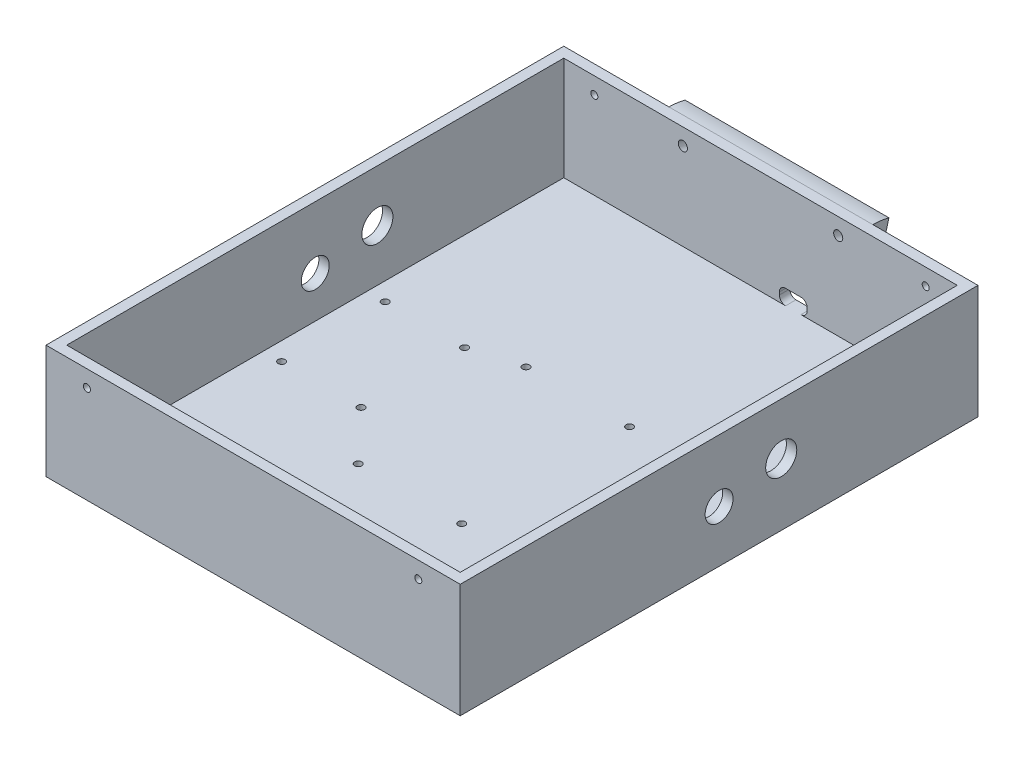
SolidWorks part; units mm, degrees
material "PLA 20%"
ref_plane "Front Plane" through (0, 0, 0) normal (0, 0, 1) x (1, 0, 0)
ref_plane "Top Plane" through (0, 0, 0) normal (0, 1, 0) x (1, 0, 0)
ref_plane "Right Plane" through (0, 0, 0) normal (1, 0, 0) x (0, 0, -1)
sketch "Sketch1" plane through (0, 0, 0) normal (0, 0, 1) x (1, 0, 0)
  line L0 (0, 50) -> (0, 0) construction
  line L1 (-95, 0) -> (95, 0)
  line L2 (-95, 0) -> (-95, 50)
  line L3 (-95, 50) -> (95, 50)
  line L4 (95, 0) -> (95, 50)
  dimension "D1" = 190
  dimension "D2" = 50
extrude "Boss-Extrude1" add sketch "Sketch1" along normal mid plane 240
shell "Shell1" thickness 5
sketch "Sketch3" plane through (100, 0, 0) normal (1, 0, 0) x (0, 0, -1)
  line L0 (-125, -5) -> (125, -5) construction
  line L1 (-15, -5) -> (15, -5)
  line L2 (-15, -5) -> (-15, 30)
  line L3 (-15, 30) -> (15, 30) construction
  line L4 (15, -5) -> (15, 30)
  line L5 (0, 30) -> (0, 20) construction
  line L6 (9.0631, 24.2262) -> (-0.618, 44.9873)
  line L7 (-15, 28.5056) -> (-9.0631, 15.7738)
  circle A0 centre (0, 20) radius 6.75
  arc A1 (-15, 30) -> (15, 30) centre (0, 30) cw
  circle A2 centre (0, 20) radius 10
  dimension "D2" = 13.5
  dimension "D5" = 20
  dimension "D1" = 25
  dimension "D3" = 30
  dimension "D4" = 10
  dimension "D6" = 25
extrude "Cut-Extrude2" cut sketch "Sketch3" against normal through all both and the other way through all contours A0
hole_wizard "M3 Clearance Hole1" positions "Sketch4" profile "Sketch5" hole size "M3" standard "ANSI Metric" end condition through all
sketch "Sketch4" plane through (0, 0, 125) normal (0, 0, 1) x (1, 0, 0)
  point P0 (-80.25, 42)
  point P1 (79.75, 42)
sketch "Sketch5" plane through (-80.25, 42, 125) normal (1, 0, 0) x (0, -1, 0)
  line L0 (0, 0) -> (0, 250)
  line L1 (0, 250) -> (1.7, 250)
  line L2 (1.7, 250) -> (1.7, 0)
  line L3 (1.7, 0) -> (0, 0)
  line L4 (0, -6.35) -> (0, 107.95) construction
  dimension "Thru Hole Dia." = 3.4
  dimension "Thru Hole Depth" = 250
sketch "Sketch8" plane through (0, 0, 0) normal (1, 0, 0) x (0, 0, -1)
  circle A0 centre (30, 25) radius 7.5
  dimension "D1" = 15
  dimension "D2" = 25
  dimension "D3" = 30
extrude "Cut-Extrude4" cut sketch "Sketch8" against normal through all both and the other way through all
sketch "Sketch10" plane through (0, 0, -125) normal (0, 0, -1) x (-1, 0, 0)
  line L0 (-100, -5) -> (-100, 50) construction
  line L5 (-22.5, 7.3) -> (-9.1, 7.3)
  line L6 (-22.5, 7.3) -> (-22.5, 0)
  line L7 (-22.5, 0) -> (-9.1, 0)
  line L8 (-9.1, 7.3) -> (-9.1, 0)
  line L9 (100, -5) -> (-100, -5) construction
  point P6 (-15.8, 0)
  dimension "D2" = 7.3
  dimension "D1" = 13.4
  dimension "D3" = 77.5
  dimension "D4" = 5
extrude "Cut-Extrude6" cut sketch "Sketch10" against normal up to surface (5 mm away) up to face at (-81.95, 42, -120)
fillet "Fillet1" radius 3 4 edges at (9.1, 0, -122.5) (22.5, 0, -122.5) (9.1, 7.3, -122.5) (22.5, 7.3, -122.5)
sketch "Sketch11" plane through (0, 0, -125) normal (0, 0, -1) x (-1, 0, 0)
  line L0 (-100, 50) -> (100, 50) construction
  line L1 (-49.2173, 20) -> (49.2173, 20)
  line L2 (-49.2173, 20) -> (-49.2173, 50)
  line L3 (-49.2173, 50) -> (49.2173, 50)
  line L4 (49.2173, 20) -> (49.2173, 50)
  line L5 (0, 0) -> (0, 50) construction
  dimension "D1" = 30
revolve "Revolve1" add sketch "Sketch11" angle 15 about L1
sketch "Sketch12" plane through (0, -29.9103, -111.6266) normal (0, -0.2588, -0.9659) x (-1, 0, 0)
  line L0 (0, 0) -> (0, 91.0316) construction
  line L1 (49.2173, 81.6709) -> (-49.2173, 81.6709) construction
  circle A0 centre (-37.5, 71.6709) radius 2.2
  dimension "D3" = 4.4
  dimension "D1" = 37.5
  dimension "D2" = 10
extrude "Cut-Extrude7" cut sketch "Sketch12" against normal up to surface (11.1249 mm away)
mirror "Mirror2" about plane through (0, 0, 0) normal (1, 0, 0) of "Cut-Extrude7"
hole_wizard "M3 Clearance Hole3" positions "Sketch16" profile "Sketch17" hole size "M3" standard "ANSI Metric"
sketch "Sketch16" plane through (0, 5, 0) normal (0, 1, 0) x (1, 0, 0)
  point P0 (-47.9032, 25)
  point P1 (-86.25, 25)
  point P2 (-47.9032, -25)
  point P3 (-86.25, -25)
  point P4 (25, -49.28)
  point P5 (47.9032, -25)
  point P6 (86.25, -25)
  point P7 (86.25, 25)
  point P8 (47.9032, 25)
  point P9 (25, 31.75)
  point P10 (-25, 31.75)
  point P11 (-25, -49.28)
sketch "Sketch17" plane through (-47.9032, 5, -25) normal (1, 0, 0) x (0, 0, 1)
  line L0 (0, 0) -> (0, 10)
  line L1 (0, 10) -> (1.7, 10)
  line L2 (1.7, 10) -> (1.7, 0)
  line L5 (1.7, 0) -> (0, 0)
  line L11 (0, -6.35) -> (0, 107.95) construction
  dimension "Thru Hole Dia." = 3.4
  dimension "Thru Hole Depth" = 10
